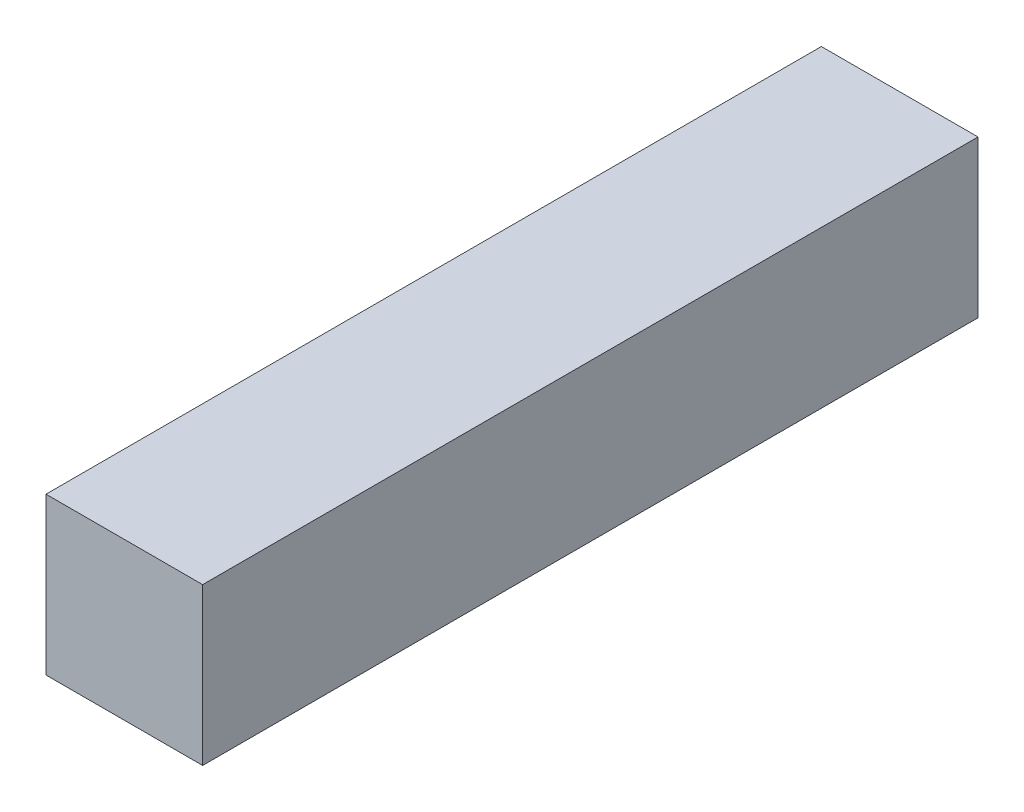
SolidWorks part; units mm, degrees
ref_plane "Front Plane" through (0, 0, 0) normal (0, 0, 1) x (1, 0, 0)
ref_plane "Top Plane" through (0, 0, 0) normal (0, 1, 0) x (1, 0, 0)
ref_plane "Right Plane" through (0, 0, 0) normal (1, 0, 0) x (0, 0, -1)
sketch "Sketch1" plane through (0, 0, 0) normal (0, 1, 0) x (1, 0, 0)
  line L1 (1, -4.95) -> (-1, -4.95)
  line L2 (1, -4.95) -> (1, 4.95)
  line L3 (1, 4.95) -> (-1, 4.95)
  line L4 (-1, -4.95) -> (-1, 4.95)
  line L5 (1, -4.95) -> (-1, 4.95) construction
  line L6 (1, 4.95) -> (-1, -4.95) construction
  point P0 (0, 0)
  dimension "D1" = 9.9
  dimension "D2" = 2
extrude "Boss-Extrude1" add sketch "Sketch1" along normal blind 2
